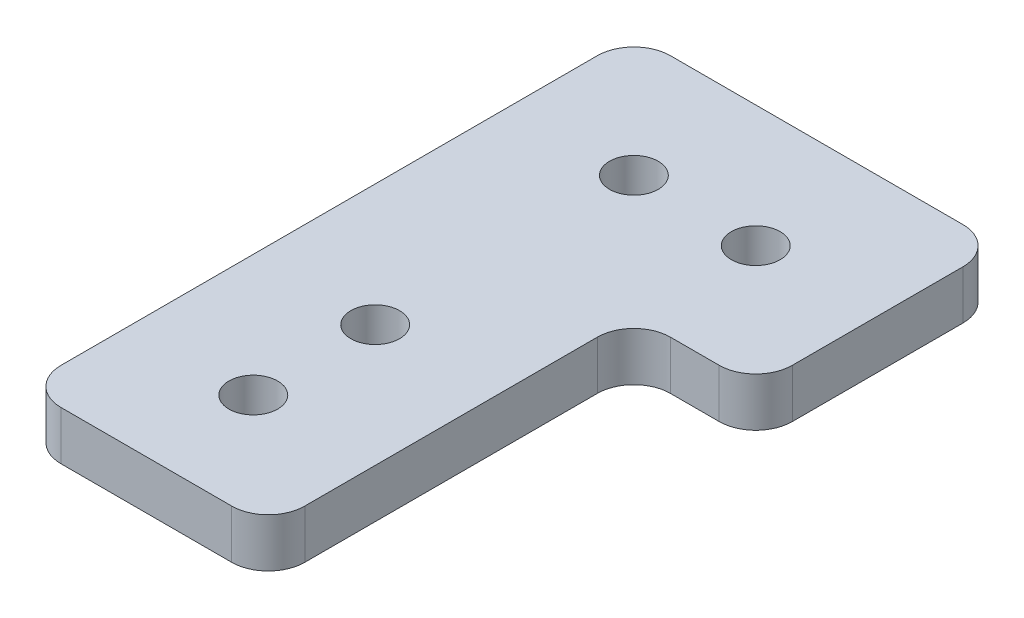
SolidWorks part; units mm, degrees
ref_plane "Front Plane" through (0, 0, 0) normal (0, 0, 1) x (1, 0, 0)
ref_plane "Top Plane" through (0, 0, 0) normal (0, 1, 0) x (1, 0, 0)
ref_plane "Right Plane" through (0, 0, 0) normal (1, 0, 0) x (0, 0, -1)
sketch "Sketch1" plane through (0, 0, 0) normal (0, 1, 0) x (1, 0, 0)
  line L0 (0, 0) -> (20, 0)
  line L1 (-55, 0) -> (55, 0) construction
  line L2 (20, 0) -> (20, 30)
  line L3 (20, 30) -> (30, 30)
  line L4 (30, 30) -> (30, 50)
  line L5 (30, 50) -> (0, 50)
  line L6 (0, -55) -> (0, 55) construction
  line L7 (0, 50) -> (0, 0)
  line L8 (20, 30) -> (0, 30) construction
  line L9 (10, 30) -> (10, 18.7732) construction
  line L10 (10, 18.7732) -> (10, 8.7732) construction
  line L11 (30, 40) -> (20, 40) construction
  line L12 (20, 40) -> (10, 40) construction
  circle A0 centre (10, 18.7732) radius 2
  circle A1 centre (10, 8.7732) radius 2
  circle A2 centre (20, 40) radius 2
  circle A3 centre (10, 40) radius 2
  dimension "D1" = 30
  dimension "D2" = 10
  dimension "D3" = 10
extrude "Boss-Extrude1" add sketch "Sketch1" along normal blind 4
fillet "Fillet1" radius 3 6 edges at (0, 2, -50) (30, 2, -50) (30, 2, -30) (20, 2, -30) (20, 2, 0) (0, 2, 0)
